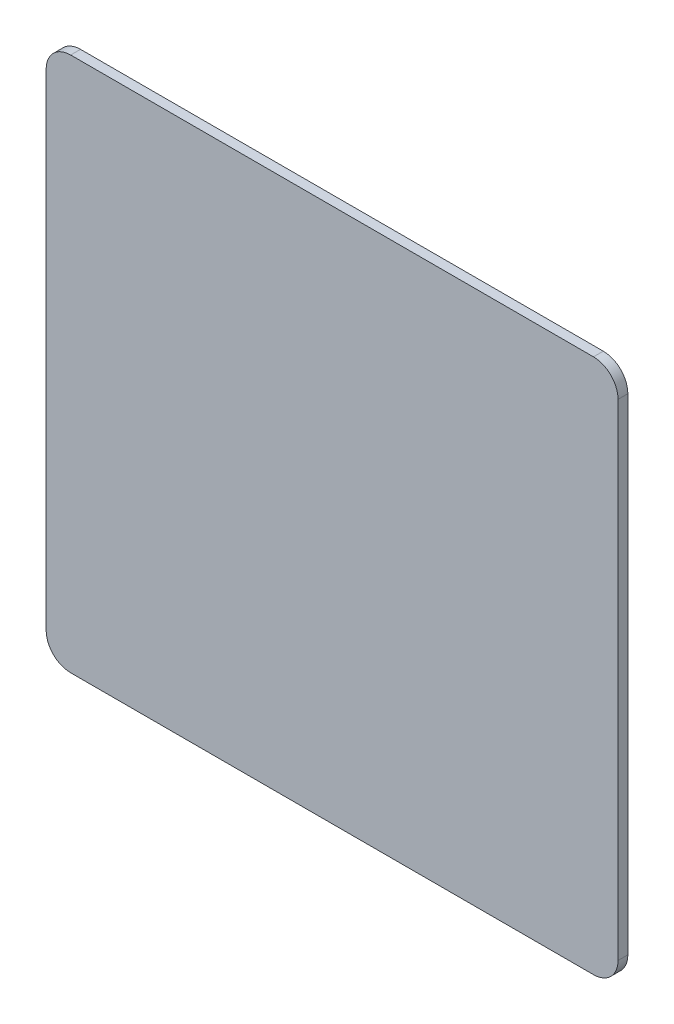
SolidWorks part; units mm, degrees
ref_plane "正面" through (0, 0, 0) normal (0, 0, 1) x (1, 0, 0)
ref_plane "平面" through (0, 0, 0) normal (0, 1, 0) x (1, 0, 0)
ref_plane "右側面" through (0, 0, 0) normal (1, 0, 0) x (0, 0, -1)
sketch "ｽｹｯﾁ1" plane through (0, 0, 0) normal (0, 0, 1) x (1, 0, 0)
  line L1 (-23.3, -21.8) -> (23.3, -21.8)
  line L2 (-23.3, -21.8) -> (-23.3, 21.8)
  line L3 (-23.3, 21.8) -> (23.3, 21.8)
  line L4 (23.3, -21.8) -> (23.3, 21.8)
  line L5 (-23.3, -21.8) -> (23.3, 21.8) construction
  line L6 (-23.3, 21.8) -> (23.3, -21.8) construction
  point P0 (0, 0)
  dimension "D1" = 46.6
  dimension "D2" = 43.6
extrude "ﾎﾞｽ - 押し出し1" add sketch "ｽｹｯﾁ1" along normal blind 0.8
fillet "ﾌｨﾚｯﾄ2" radius 2 4 edges at (-23.3, 21.8, 0.4) (23.3, 21.8, 0.4) (-23.3, -21.8, 0.4) (23.3, -21.8, 0.4)
